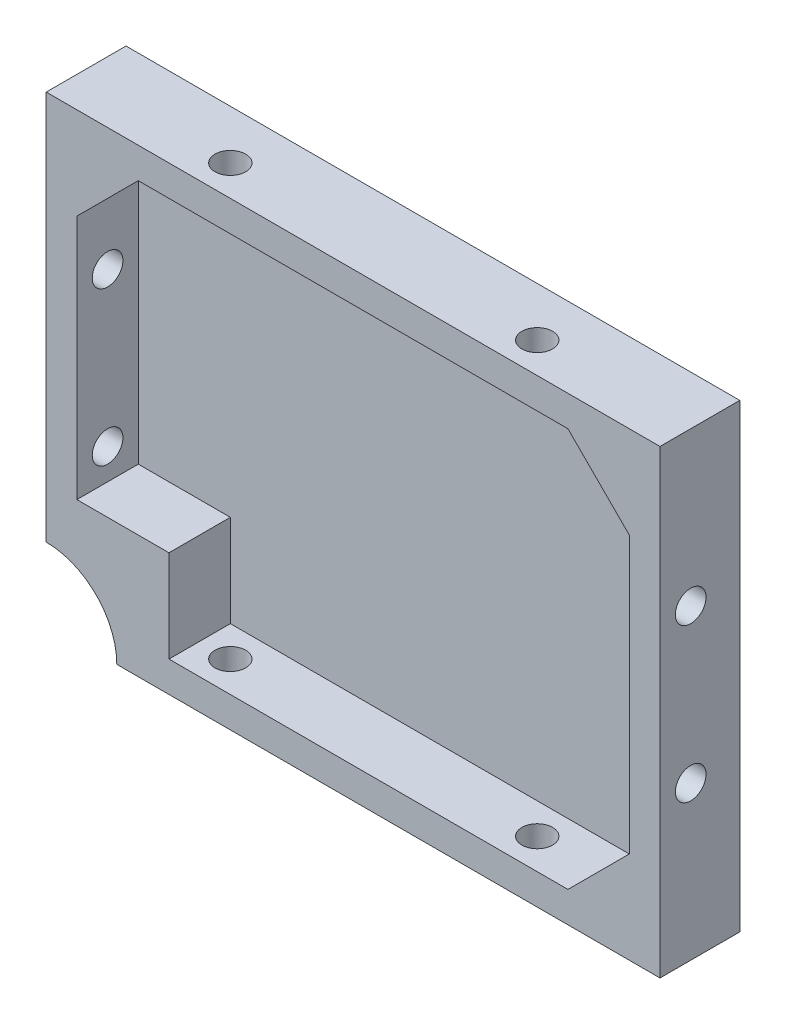
SolidWorks part; units mm, degrees
ref_plane "Plan de face" through (0, 0, 0) normal (0, 0, 1) x (1, 0, 0)
ref_plane "Plan de dessus" through (0, 0, 0) normal (0, 1, 0) x (1, 0, 0)
ref_plane "Plan de droite" through (0, 0, 0) normal (1, 0, 0) x (0, 0, -1)
sketch "Esquisse1" plane through (0, 0, 0) normal (0, 0, 1) x (1, 0, 0)
  line L0 (44.1184, 33.7284) -> (54.1184, 33.7284)
  line L1 (-45.8816, 33.7284) -> (44.1184, 33.7284)
  line L2 (-45.8816, 33.7284) -> (-45.8816, -41.2716)
  line L3 (-45.8816, -41.2716) -> (54.1184, -41.2716)
  line L4 (54.1184, 23.7284) -> (54.1184, -41.2716)
  line L5 (54.1184, 33.7284) -> (54.1184, 23.7284)
  point P6 (54.1184, 33.7284)
  dimension "D1" = 100
  dimension "D2" = 75
extrude "Boss.-Extru.1" add sketch "Esquisse1" along normal blind 13
shell "Coque1" thickness 5
sketch "Esquisse2" plane through (-45.8816, 0, 0) normal (-1, 0, 0) x (0, 0, 1)
  line L0 (13, 33.7284) -> (13, -41.2716) construction
  line L1 (13, 33.7284) -> (0, 33.7284) construction
  line L2 (13, -41.2716) -> (0, -41.2716) construction
  circle A0 centre (8, 8.7284) radius 2.5
  circle A1 centre (8, -16.2716) radius 2.5
  dimension "D1" = 5
  dimension "D2" = 5
  dimension "D3" = 5
  dimension "D4" = 5
  dimension "D5" = 25
  dimension "D6" = 25
extrude "Enlèv. mat.-Extru.1" cut sketch "Esquisse2" against normal up to surface (100 mm away) contours A1 | A0 up to face at (54.1184, -3.7716, 6.5)
sketch "Esquisse3" plane through (0, -41.2716, 0) normal (0, -1, 0) x (1, 0, 0)
  line L0 (-45.8816, 13) -> (54.1184, 13) construction
  line L2 (54.1184, 13) -> (54.1184, 0) construction
  line L3 (-45.8816, 13) -> (-45.8816, 0) construction
  circle A0 centre (-20.8816, 8) radius 2.5
  circle A1 centre (29.1184, 8) radius 2.5
  dimension "D1" = 5
  dimension "D2" = 5
  dimension "D3" = 5
  dimension "D4" = 5
  dimension "D5" = 25
  dimension "D6" = 25
extrude "Enlèv. mat.-Extru.2" cut sketch "Esquisse3" against normal up to surface (75 mm away) up to face at (4.1184, 33.7284, 6.5)
sketch "Esquisse4" plane through (0, 0, 3) normal (0, 0, 1) x (1, 0, 0)
  line L0 (-30.8816, 28.7284) -> (-40.8816, 18.7284)
  line L1 (49.1184, 28.7284) -> (-40.8816, 28.7284) construction
  line L2 (-40.8816, 28.7284) -> (-40.8816, -36.2716) construction
  line L3 (-40.8816, 18.7284) -> (-40.8816, 28.7284)
  line L4 (-40.8816, 28.7284) -> (-30.8816, 28.7284)
  line L5 (49.1184, 28.7284) -> (49.1184, 18.7284)
  line L6 (49.1184, -36.2716) -> (49.1184, 28.7284) construction
  line L7 (49.1184, 18.7284) -> (39.1184, 28.7284)
  line L8 (39.1184, 28.7284) -> (49.1184, 28.7284)
  line L9 (49.1184, 28.7284) -> (-40.8816, 28.7284) construction
  line L10 (49.1184, -36.2716) -> (49.1184, -26.2716)
  line L11 (49.1184, -26.2716) -> (39.1184, -36.2716)
  line L12 (-40.8816, -36.2716) -> (49.1184, -36.2716) construction
  line L13 (39.1184, -36.2716) -> (49.1184, -36.2716)
  line L14 (-40.8816, -21.2716) -> (-25.8816, -21.2716)
  line L16 (-40.8816, 28.7284) -> (-40.8816, -36.2716) construction
  line L17 (-25.8816, -21.2716) -> (-25.8816, -36.2716)
  line L18 (-25.8816, -36.2716) -> (-40.8816, -36.2716)
  line L19 (-40.8816, -36.2716) -> (-40.8816, -21.2716)
  dimension "D1" = 10
  dimension "D2" = 10
  dimension "D3" = 10
  dimension "D4" = 10
  dimension "D5" = 10
  dimension "D6" = 10
  dimension "D7" = 15
  dimension "D8" = 15
extrude "Boss.-Extru.2" add sketch "Esquisse4" along normal up to surface (10 mm away) up to face at (4.1184, -3.7716, 13)
sketch "Esquisse6" plane through (0, 0, 13) normal (0, 0, 1) x (1, 0, 0)
  circle A0 centre (-45.8816, -41.2716) radius 11.5
  dimension "D1" = 23
extrude "Enlèv. mat.-Extru.4" cut sketch "Esquisse6" against normal up to surface (13 mm away) up to face at (4.1184, -3.7716, 0)
